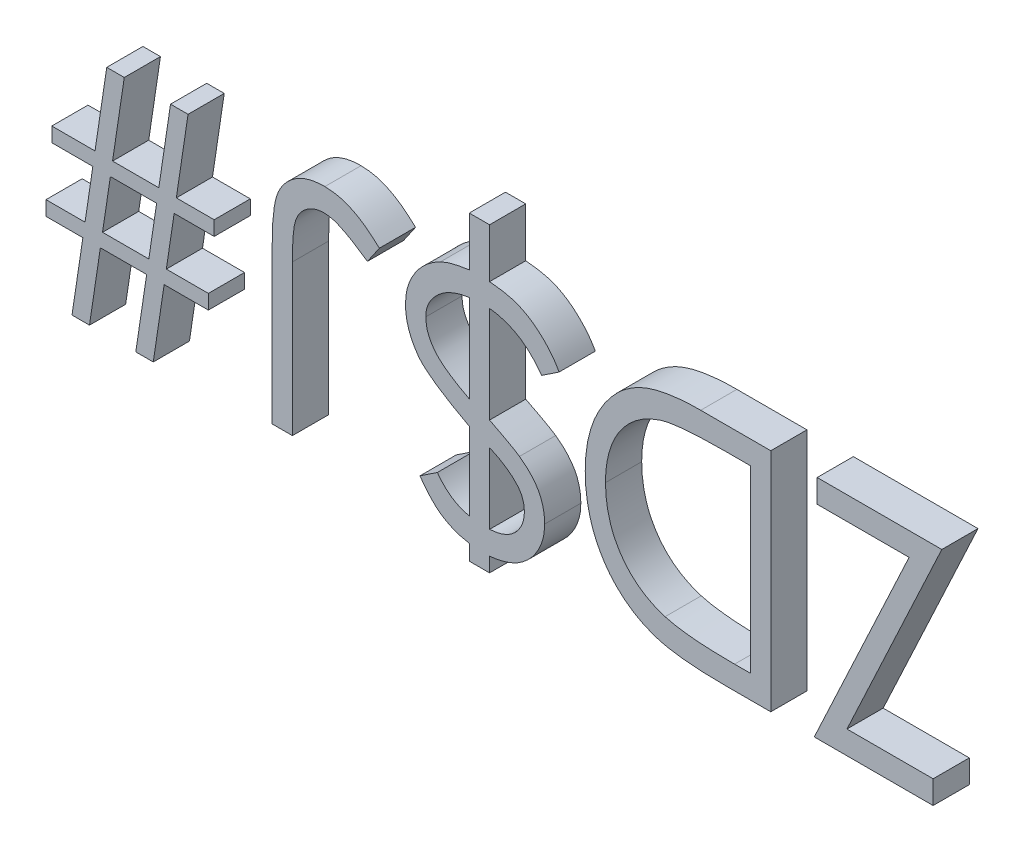
SolidWorks part; units mm, degrees
ref_plane "Front Plane" through (0, 0, 0) normal (0, 0, 1) x (1, 0, 0)
ref_plane "Top Plane" through (0, 0, 0) normal (0, 1, 0) x (1, 0, 0)
ref_plane "Right Plane" through (0, 0, 0) normal (1, 0, 0) x (0, 0, -1)
sketch "Sketch1" plane through (0, 0, 0) normal (0, 0, 1) x (1, 0, 0)
  line L0 (35.56, 0) -> (-35.56, 0) construction
  text T0 "ZD$J#" font "Century Gothic" height in points 60
  point P4 (0, 0)
  dimension "D1" = 71.12
extrude "Boss-Extrude1" add sketch "Sketch1" along normal blind 2.54
